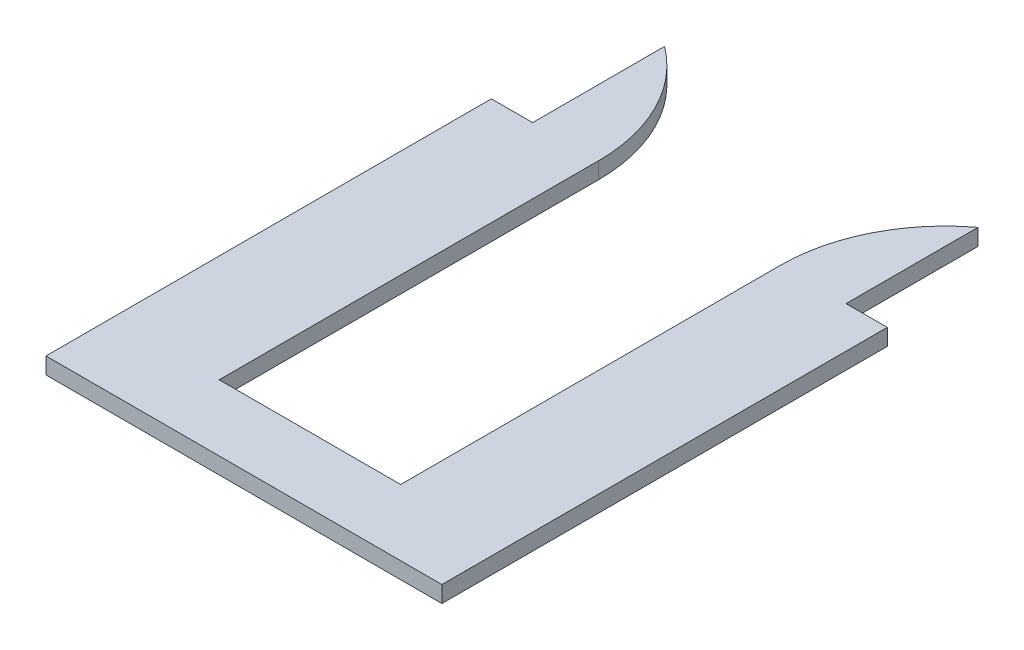
SolidWorks part; units mm, degrees
ref_plane "Front Plane" through (0, 0, 0) normal (0, 0, 1) x (1, 0, 0)
ref_plane "Top Plane" through (0, 0, 0) normal (0, 1, 0) x (1, 0, 0)
ref_plane "Right Plane" through (0, 0, 0) normal (1, 0, 0) x (0, 0, -1)
sketch "Sketch2" plane through (0, 0, 0) normal (0, 1, 0) x (1, 0, 0)
  line L0 (0, 0) -> (304.8, 0)
  line L1 (304.8, 0) -> (304.8, 342.9)
  line L2 (304.8, 342.9) -> (273.05, 342.9)
  line L3 (273.05, 342.9) -> (273.05, 444.5)
  line L4 (273.05, 444.5) -> (222.25, 342.9) construction
  line L5 (222.25, 342.9) -> (222.25, 50.8)
  line L6 (0, 0) -> (0, 342.9)
  line L7 (0, 342.9) -> (31.75, 342.9)
  line L8 (31.75, 342.9) -> (31.75, 444.5)
  line L9 (31.75, 444.5) -> (82.55, 342.9) construction
  line L10 (82.55, 342.9) -> (82.55, 50.8)
  line L11 (82.55, 50.8) -> (222.25, 50.8)
  line L12 (304.8, 342.9) -> (273.05, 342.9) construction
  line L13 (273.05, 342.9) -> (222.25, 342.9) construction
  line L14 (82.55, 342.9) -> (31.75, 342.9) construction
  line L15 (222.25, 342.9) -> (82.55, 342.9) construction
  arc A0 (31.75, 444.5) -> (82.55, 342.9) centre (-44.45, 342.9) cw
  arc A1 (273.05, 444.5) -> (222.25, 342.9) centre (349.25, 342.9) ccw
  dimension "D1" = 342.9
  dimension "D2" = 304.8
  dimension "D3" = 82.55
  dimension "D4" = 82.55
  dimension "D5" = 50.8
  dimension "D6" = 31.75
  dimension "D7" = 31.75
  dimension "D8" = 101.6
  dimension "D9" = 101.6
extrude "Boss-Extrude1" add sketch "Sketch2" along normal blind 12.7
